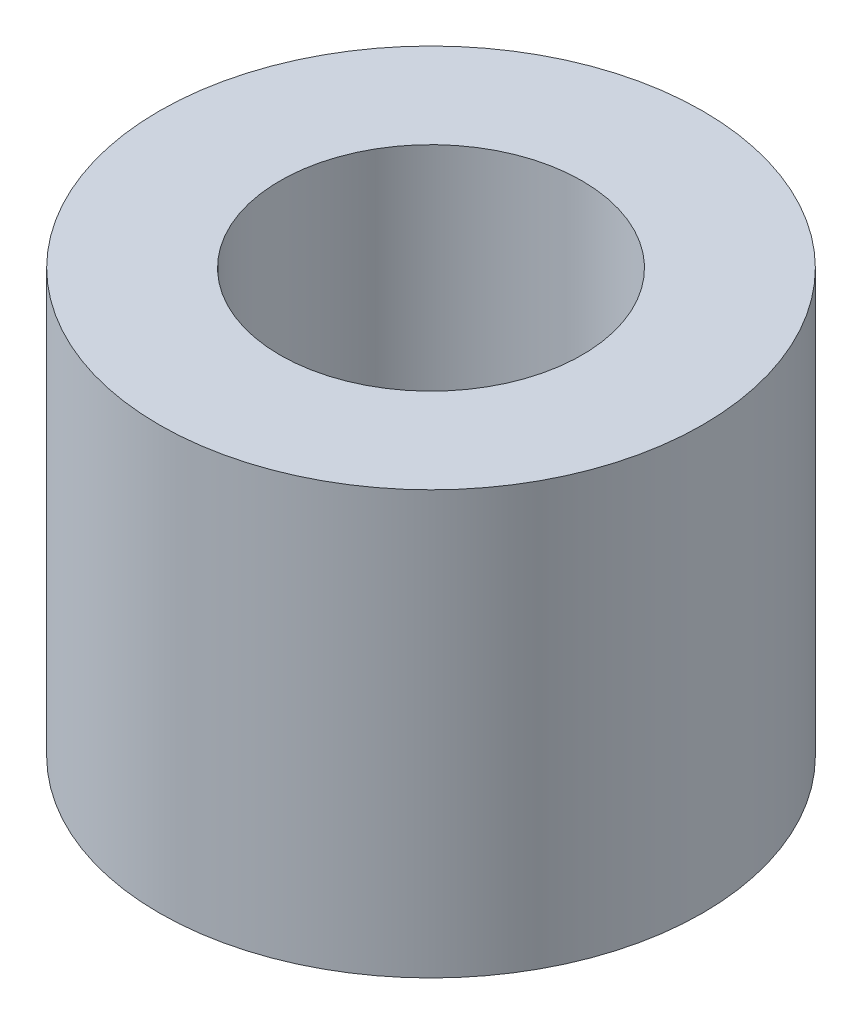
SolidWorks part; units mm, degrees
ref_plane "前视基准面" through (0, 0, 0) normal (0, 0, 1) x (1, 0, 0)
ref_plane "上视基准面" through (0, 0, 0) normal (0, 1, 0) x (1, 0, 0)
ref_plane "右视基准面" through (0, 0, 0) normal (1, 0, 0) x (0, 0, -1)
sketch "草图1" plane through (0, 0, 0) normal (0, 1, 0) x (1, 0, 0)
  circle A0 centre (0, 0) radius 2.5
  circle A1 centre (0, 0) radius 4.5
  dimension "D1" = 5
  dimension "D2" = 9
extrude "凸台-拉伸1" add sketch "草图1" along normal blind 7
